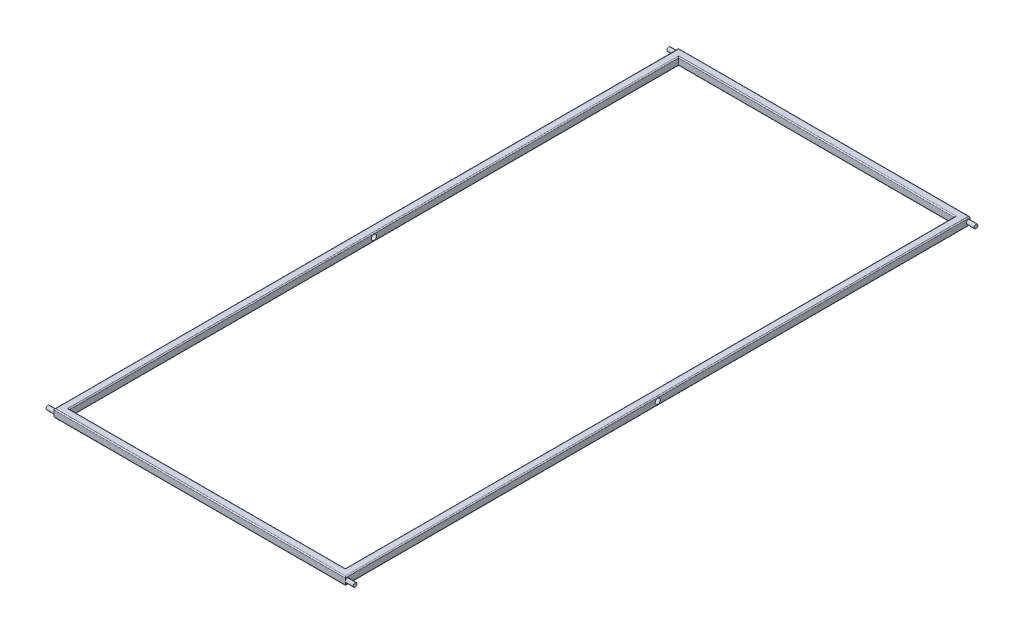
SolidWorks part; units mm, degrees
ref_plane "Alzado" through (0, 0, 0) normal (0, 0, 1) x (1, 0, 0)
ref_plane "Planta" through (0, 0, 0) normal (0, 1, 0) x (1, 0, 0)
ref_plane "Vista lateral" through (0, 0, 0) normal (1, 0, 0) x (0, 0, -1)
sketch "Croquis1" plane through (0, 0, 0) normal (0, 1, 0) x (1, 0, 0)
  line L1 (-280, -600) -> (280, -600)
  line L2 (-280, -600) -> (-280, 600)
  line L3 (-280, 600) -> (280, 600)
  line L4 (280, -600) -> (280, 600)
  line L5 (-280, -600) -> (280, 600) construction
  line L6 (-280, 600) -> (280, -600) construction
  line L7 (-265, -585) -> (265, -585)
  line L8 (-265, -585) -> (-265, 585)
  line L9 (-265, 585) -> (265, 585)
  line L10 (265, -585) -> (265, 585)
  line L11 (-265, -585) -> (265, 585) construction
  line L12 (-265, 585) -> (265, -585) construction
  point P0 (0, 0)
  point P6 (0, 0)
  dimension "D1" = 1200
  dimension "D2" = 560
  dimension "D3" = 530
  dimension "D4" = 1170
extrude "Saliente-Extruir1" add sketch "Croquis1" along normal blind 15
fillet "Redondeo1" radius 2 8 edges at (0, 15, 585) (-265, 15, 0) (0, 15, -585) (265, 15, 0) (280, 15, 0) (0, 15, 600) (-280, 15, 0) (0, 15, -600)
fillet "Redondeo2" radius 2 8 edges at (-265, 0, 0) (0, 0, -585) (265, 0, 0) (0, 0, 585) (0, 0, -600) (-280, 0, 0) (0, 0, 600) (280, 0, 0)
sketch "Croquis2" plane through (-280, 0, 0) normal (-1, 0, 0) x (0, 0, 1)
  line L0 (0, 2) -> (0, 13) construction
  line L1 (-600, 2) -> (600, 2) construction
  line L2 (600, 13) -> (-600, 13) construction
  line L3 (596.25, 2) -> (596.25, 7.5) construction
  line L5 (600, 13) -> (600, 2) construction
  line L6 (596.25, 7.5) -> (600, 7.5) construction
  circle A0 centre (596.25, 7.5) radius 3.75
  circle A1 centre (-596.25, 7.5) radius 3.75
  dimension "D2" = 7.5
  dimension "D1" = 3.75
extrude "Saliente-Extruir2" add sketch "Croquis2" along normal blind 15
mirror "Simetría1" about plane through (0, 0, 0) normal (1, 0, 0) of "Saliente-Extruir2"
sketch "Croquis3" plane through (-280, 0, 0) normal (-1, 0, 0) x (0, 0, 1)
  line L0 (0, 2) -> (0, 13) construction
  line L1 (-600, 2) -> (600, 2) construction
  line L2 (600, 13) -> (-600, 13) construction
  circle A0 centre (0, 7.5) radius 5
  dimension "D1" = 10
extrude "Cortar-Extruir1" cut sketch "Croquis3" against normal through all
scale "Escala1" scale about origin uniform scaling yes scale factor 1.3
